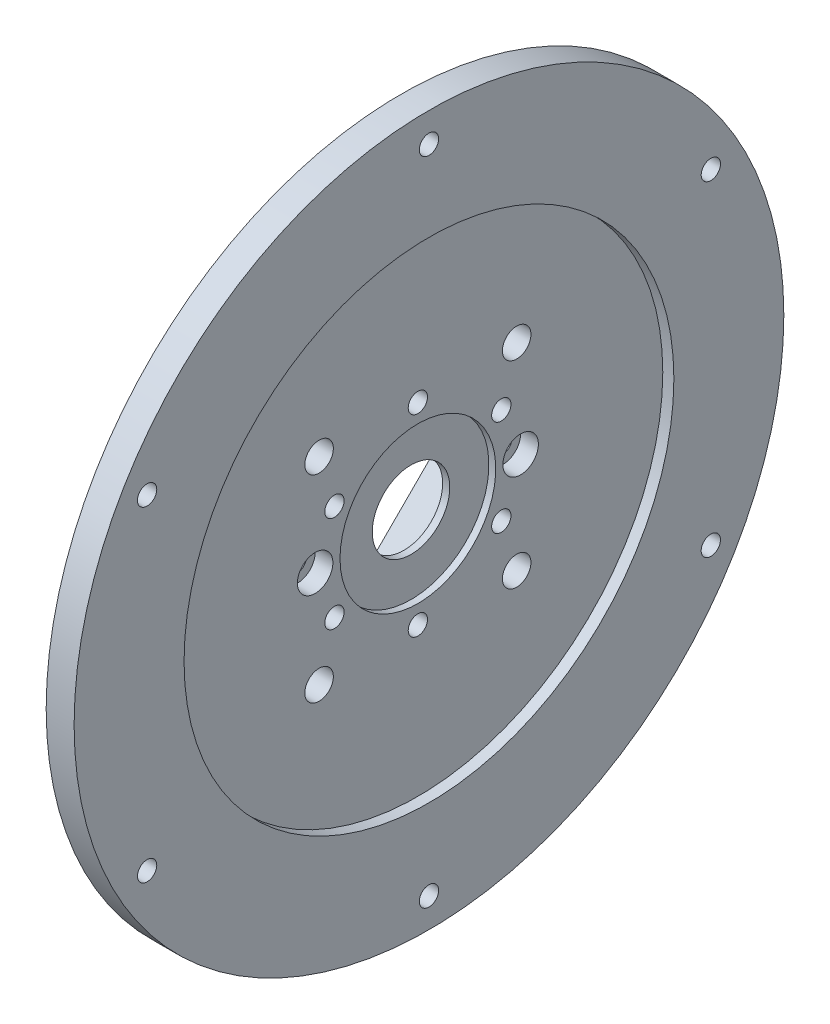
SolidWorks part; units mm, degrees
ref_plane "Front Plane" through (0, 0, 0) normal (0, 0, 1) x (1, 0, 0)
ref_plane "Top Plane" through (0, 0, 0) normal (0, 1, 0) x (1, 0, 0)
ref_plane "Right Plane" through (0, 0, 0) normal (1, 0, 0) x (0, 0, -1)
sketch "Sketch1" plane through (0, 0, 0) normal (0, 0, 1) x (1, 0, 0)
  line L0 (0, 0) -> (58.591, 0) construction
  line L2 (0, 0) -> (18.4, 0)
  line L3 (0, 0) -> (0, 2.5)
  line L4 (0, 2.5) -> (18.4, 2.5)
  line L5 (18.4, 0) -> (18.4, 2.5)
  line L6 (6.0094, 2.5) -> (6.0094, 6)
  line L11 (6.0094, 6) -> (9.9794, 6)
  line L16 (12.9794, 6) -> (12.9794, 3)
  line L17 (12.9794, 3) -> (13.6398, 3)
  line L18 (13.6398, 3) -> (13.6398, 2.5)
  line L19 (13.6398, 2.5) -> (6.0094, 2.5)
  line L22 (13.6398, 2.5) -> (16.1198, 2.5)
  line L23 (13.6398, 2.5) -> (13.6398, 4)
  line L24 (13.6398, 4) -> (16.1198, 4)
  line L25 (16.1198, 2.5) -> (16.1198, 4)
  line L27 (6.0094, 6) -> (9.9794, 6)
  line L28 (6.0094, 6) -> (6.0094, 9)
  line L29 (6.0094, 9) -> (9.9794, 9)
  line L30 (9.9794, 6) -> (9.9794, 9)
  line L31 (6.0094, 9) -> (6.0094, 8.25)
  line L32 (6.0094, 8.25) -> (5.0094, 8.25)
  line L33 (8.6609, 22.001) -> (8.6609, 12.476) construction
  line L34 (5.0094, 12.476) -> (12.3124, 12.476)
  line L35 (9.9794, 9) -> (12.3124, 9)
  line L36 (5.0094, 7.9375) -> (1.7709, 7.9375)
  line L37 (5.0094, 8.25) -> (5.0094, 12.476)
  line L38 (5.0094, 7.9375) -> (5.0094, 13.9365)
  line L39 (5.0094, 13.9365) -> (1.7709, 13.9365)
  line L40 (1.7709, 7.9375) -> (1.7709, 13.9365)
  line L41 (5.0094, 22.001) -> (12.3124, 22.001)
  line L42 (5.0094, 22.001) -> (5.0094, 30.1625)
  line L43 (5.0094, 30.1625) -> (12.3124, 30.1625)
  line L44 (12.3124, 22.001) -> (12.3124, 30.1625)
  line L49 (16.6398, 22.001) -> (16.6398, 7.5)
  line L51 (23.0198, 7.5) -> (23.0198, 6.5)
  line L54 (16.1198, 4) -> (13.6398, 4)
  line L56 (18.0398, 7.5) -> (23.0198, 7.5)
  line L57 (13.3124, 22.001) -> (16.6398, 22.001)
  line L58 (16.1198, 3.5) -> (20.0198, 3.5)
  line L59 (29.9098, 14) -> (26.9098, 11)
  line L60 (4.0094, 31.75) -> (18.0398, 31.75)
  line L61 (18.0398, 7.5) -> (23.0198, 7.5)
  line L62 (18.0398, 7.5) -> (18.0398, 12)
  line L63 (18.0398, 12) -> (23.0198, 12)
  line L64 (23.0198, 7.5) -> (23.0198, 12)
  line L65 (18.0398, 31.75) -> (18.0398, 12)
  line L66 (23.0198, 11) -> (26.9098, 11)
  line L67 (34.8098, 23) -> (31.3098, 19.5)
  line L68 (35.8098, 31) -> (38.7998, 33.99)
  line L69 (29.9098, 14) -> (29.9098, 15)
  line L70 (29.9098, 15) -> (22.9398, 15)
  line L71 (22.9398, 15) -> (21.0398, 15)
  line L72 (18.0398, 7.5) -> (16.6398, 7.5)
  line L73 (21.0398, 15) -> (21.0398, 43)
  line L74 (19.6115, 40) -> (9.6516, 40)
  line L75 (9.6516, 40) -> (4.0094, 40)
  line L76 (21.0398, 43) -> (19.6115, 43)
  line L77 (22.9398, 15) -> (29.9098, 15)
  line L78 (22.9398, 15) -> (22.9398, 21)
  line L79 (22.9398, 21) -> (29.9098, 21)
  line L80 (29.9098, 15) -> (29.9098, 21)
  line L81 (9.6516, 40) -> (19.6115, 40)
  line L82 (9.6516, 40) -> (9.6516, 50)
  line L83 (9.6516, 50) -> (19.6115, 50)
  line L84 (19.6115, 40) -> (19.6115, 50)
  line L85 (4.0094, 40) -> (4.0094, 31.75)
  line L86 (12.9794, 3) -> (12.9794, 2.5)
  line L87 (31.3098, 19.5) -> (29.9098, 19.5)
  line L88 (21.4694, 63.5) -> (21.4694, 51.308)
  line L89 (21.4694, 63.5) -> (25.9398, 63.5)
  line L90 (25.9398, 63.5) -> (25.9398, 25)
  line L91 (27.8398, 25) -> (25.9398, 25)
  line L92 (9.6516, 48) -> (8.2233, 48)
  line L93 (8.2233, 48) -> (8.2233, 53.476)
  line L94 (8.2233, 53.476) -> (19.6115, 53.476)
  line L95 (19.6115, 53.476) -> (19.6115, 50)
  line L96 (13.9174, 63.001) -> (13.9174, 53.476) construction
  line L97 (8.2233, 63.001) -> (19.6115, 63.001)
  line L98 (8.2233, 63.001) -> (8.2233, 68.2625)
  line L99 (8.2233, 68.2625) -> (19.6115, 68.2625)
  line L100 (19.6115, 63.001) -> (19.6115, 68.2625)
  line L101 (12.9794, 6) -> (11.9794, 6)
  line L102 (8.2233, 44.825) -> (4.9848, 44.825)
  line L103 (8.2233, 44.825) -> (8.2233, 54.9365)
  line L104 (8.2233, 54.9365) -> (4.9848, 54.9365)
  line L106 (9.9794, 6) -> (10.8794, 6)
  line L107 (27.8398, 25) -> (34.8098, 25)
  line L108 (34.8098, 25) -> (34.8098, 23)
  line L109 (0, 0) -> (-2, 0)
  line L110 (0, 0) -> (0, 11)
  line L111 (27.8398, 25) -> (34.8098, 25)
  line L112 (27.8398, 25) -> (27.8398, 32.5)
  line L113 (27.8398, 32.5) -> (34.8098, 32.5)
  line L114 (34.8098, 25) -> (34.8098, 32.5)
  line L115 (35.8098, 31) -> (34.8098, 31)
  line L116 (27.8398, 32.5) -> (27.8398, 64.5)
  line L117 (20.5849, 74.025) -> (6.2499, 74.025)
  line L118 (6.2499, 74.025) -> (6.2499, 76.2)
  line L119 (38.7998, 47.29) -> (30.8398, 55.25)
  line L120 (0, 11) -> (-2, 11)
  line L121 (38.7998, 43.815) -> (30.8623, 43.815)
  line L123 (-4.8152, 69.85) -> (1.5348, 76.2)
  line L124 (38.7998, 47.29) -> (38.7998, 33.99)
  line L125 (-2, 0) -> (-2, 11)
  line L126 (38.7998, 37.465) -> (30.8623, 37.465)
  line L127 (30.8623, 43.815) -> (30.8623, 37.465)
  line L128 (6.0094, 2.5) -> (6.0094, 0)
  line L129 (-0.0152, 63.5) -> (-0.0152, 30)
  line L132 (4.9848, 63.5) -> (-0.0152, 63.5)
  line L136 (-1.8152, 30) -> (-11.7752, 30)
  line L138 (-13.7752, 25.4) -> (-2, 25.4)
  line L139 (-2, 25.4) -> (-2, 11.5)
  line L140 (27.8398, 64.5) -> (20.5849, 64.5)
  line L141 (-1.8152, 30) -> (-11.7752, 30)
  line L142 (-1.8152, 30) -> (-1.8152, 39)
  line L143 (-1.8152, 39) -> (-11.7752, 39)
  line L144 (-11.7752, 30) -> (-11.7752, 39)
  line L145 (20.5849, 64.5) -> (20.5849, 74.025)
  line L146 (-12.7752, 37) -> (-12.7752, 47.29)
  line L147 (-12.7752, 37) -> (-11.7752, 37)
  line L148 (30.8398, 55.25) -> (30.8398, 76.2)
  line L149 (11.9794, 6) -> (11.9794, 5.45)
  line L154 (-2, 11.5) -> (0.5, 11.5)
  line L155 (4.9848, 60.6197) -> (24.0348, 60.6197)
  line L160 (4.9848, 60.6197) -> (4.9848, 55.8572)
  line L161 (4.9848, 55.8572) -> (24.0348, 55.8572)
  line L166 (24.0348, 60.6197) -> (24.0348, 55.8572)
  line L167 (4.9848, 60.6197) -> (24.0348, 55.8572) construction
  line L172 (4.9848, 55.8572) -> (24.0348, 60.6197) construction
  line L173 (24.0348, 62.2072) -> (25.9398, 62.2072)
  line L174 (11.9794, 5.45) -> (10.8794, 5.45)
  line L175 (10.8794, 6) -> (10.8794, 5.45)
  line L176 (24.0348, 62.2072) -> (24.0348, 54.2697)
  line L177 (24.0348, 54.2697) -> (25.9398, 54.2697)
  line L178 (25.9398, 62.2072) -> (25.9398, 54.2697)
  line L179 (24.0348, 62.2072) -> (25.9398, 54.2697) construction
  line L180 (24.0348, 54.2697) -> (25.9398, 62.2072) construction
  line L181 (3, 19.6197) -> (15.7, 19.6197)
  line L182 (3, 19.6197) -> (3, 14.8572)
  line L183 (3, 14.8572) -> (15.7, 14.8572)
  line L184 (15.7, 19.6197) -> (15.7, 14.8572)
  line L185 (3, 19.6197) -> (15.7, 14.8572) construction
  line L186 (3, 14.8572) -> (15.7, 19.6197) construction
  line L187 (15.7, 21.2072) -> (16.6398, 21.2072)
  line L188 (15.7, 21.2072) -> (15.7, 13.2697)
  line L189 (15.7, 13.2697) -> (16.6398, 13.2697)
  line L190 (16.6398, 21.2072) -> (16.6398, 13.2697)
  line L191 (15.7, 21.2072) -> (16.6398, 13.2697) construction
  line L192 (15.7, 13.2697) -> (16.6398, 21.2072) construction
  line L193 (0.5, 11.5) -> (0.5, 6.9375)
  line L194 (0.5, 6.9375) -> (1.7709, 6.9375)
  line L195 (23.0198, 6.5) -> (20.0198, 3.5)
  line L196 (4.9848, 63.5) -> (4.9848, 54.9365)
  line L197 (3, 43.825) -> (4.9848, 43.825)
  line L198 (1.7709, 6.9375) -> (1.7709, 7.9375)
  line L199 (6.0094, 0) -> (12.9794, 0)
  line L200 (12.9794, 0) -> (12.9794, 2.5)
  line L201 (18.0398, 31.75) -> (18.0398, 35.875)
  line L202 (18.0398, 35.875) -> (21.0398, 35.875)
  line L203 (30.8398, 76.2) -> (6.2499, 76.2)
  line L204 (2.8049, 69.85) -> (7.2499, 69.85) construction
  line L205 (7.2499, 67.4688) -> (26.2999, 67.4688)
  line L206 (7.2499, 74.025) -> (7.2499, 64.5)
  line L207 (7.2499, 64.5) -> (-1.8152, 64.5)
  line L208 (-1.8152, 64.5) -> (-1.8152, 39)
  line L209 (-12.7752, 47.29) -> (-4.8152, 55.25)
  line L210 (-4.8152, 55.25) -> (-4.8152, 69.85)
  line L211 (7.2499, 67.4688) -> (7.2499, 72.2312)
  line L212 (7.2499, 72.2312) -> (26.2999, 72.2313)
  line L213 (26.2999, 67.4688) -> (26.2999, 72.2313)
  line L214 (26.2999, 73.8187) -> (30.8398, 73.8187)
  line L215 (26.2999, 73.8187) -> (26.2999, 65.8813)
  line L216 (26.2999, 65.8813) -> (30.8398, 65.8813)
  line L217 (30.8398, 73.8187) -> (30.8398, 65.8813)
  line L218 (2.8049, 72.2313) -> (25.0299, 72.2313)
  line L219 (2.8049, 72.2313) -> (2.8049, 67.4687)
  line L220 (2.8049, 67.4687) -> (25.0299, 67.4687)
  line L221 (25.0299, 72.2313) -> (25.0299, 67.4687)
  line L222 (25.0299, 69.85) -> (20.5849, 69.85) construction
  line L223 (21.4694, 51.308) -> (22.9398, 51.308)
  line L224 (22.9398, 51.308) -> (22.9398, 21)
  line L225 (13.6398, 4) -> (13.6398, 12.2697)
  line L226 (13.6398, 12.2697) -> (13.3124, 12.2697)
  line L227 (13.3124, 12.2697) -> (13.3124, 22.001)
  line L228 (12.3124, 9) -> (12.3124, 12.476)
  line L229 (-1.8152, 30) -> (-0.0152, 30)
  line L230 (8.2233, 65.6317) -> (2.8049, 65.6317) construction
  line L231 (19.6115, 65.6317) -> (25.0299, 65.6317) construction
  line L232 (1.5348, 76.2) -> (6.2499, 76.2)
  line L233 (-11.7752, 30) -> (-13.7752, 30)
  line L234 (-13.7752, 30) -> (-13.7752, 25.4)
  line L235 (3, 13.9365) -> (3, 43.825)
  line L236 (4.9848, 54.9365) -> (4.9848, 44.825)
  line L237 (4.9848, 43.825) -> (4.9848, 44.825)
  circle A0 centre (26.8898, 25.95) radius 0.95
  circle A1 centre (21.9898, 15.95) radius 0.95
  circle A2 centre (17.3398, 8.2) radius 0.7
  circle A3 centre (10.4294, 6.45) radius 0.45
  circle A4 centre (-0.9152, 30.9) radius 0.9
  point P7 (24.9873, 58.2385)
  point P131 (16.1699, 17.2385)
  point P135 (14.5098, 58.2385)
  point P146 (9.35, 17.2385)
sketch "Sketch2" plane through (0, 0, 0) normal (0, 0, 1) x (1, 0, 0)
  line L0 (-1.8152, 30) -> (-11.7752, 30) construction
  line L1 (-2, 25.4) -> (-2, 11.5) construction
  line L3 (-13.7752, 25.4) -> (-2, 25.4) construction
  line L4 (-2, 11.5) -> (0.5, 11.5) construction
  line L5 (0.5, 11.5) -> (0.5, 6.9375) construction
  line L6 (0.5, 6.9375) -> (1.7709, 6.9375) construction
  line L10 (4.9848, 63.5) -> (-0.0152, 63.5) construction
  line L11 (-0.0152, 63.5) -> (-0.0152, 30) construction
  line L14 (-1.8152, 30) -> (-11.7752, 30)
  line L15 (-2, 25.4) -> (-2, 11.5)
  line L17 (-13.7752, 25.4) -> (-2, 25.4)
  line L18 (-2, 11.5) -> (0.5, 11.5)
  line L19 (0.5, 11.5) -> (0.5, 6.9375)
  line L20 (0.5, 6.9375) -> (1.7709, 6.9375)
  line L24 (4.9848, 63.5) -> (-0.0152, 63.5)
  line L25 (-0.0152, 63.5) -> (-0.0152, 30)
  line L28 (-1.8152, 30) -> (-0.0152, 30) construction
  line L29 (-1.8152, 30) -> (-0.0152, 30)
  line L30 (-13.7752, 30) -> (-13.7752, 25.4) construction
  line L31 (-11.7752, 30) -> (-13.7752, 30) construction
  line L32 (-13.7752, 30) -> (-13.7752, 25.4)
  line L33 (-11.7752, 30) -> (-13.7752, 30)
  line L34 (1.7709, 6.9375) -> (1.7709, 7.9375) construction
  line L35 (1.7709, 7.9375) -> (1.7709, 13.9365) construction
  line L36 (5.0094, 13.9365) -> (1.7709, 13.9365) construction
  line L37 (3, 13.9365) -> (3, 43.825) construction
  line L40 (4.9848, 63.5) -> (4.9848, 54.9365) construction
  line L41 (1.7709, 6.9375) -> (1.7709, 7.9375)
  line L42 (1.7709, 7.9375) -> (1.7709, 13.9365)
  line L43 (3, 13.9365) -> (1.7709, 13.9365)
  line L44 (3, 13.9365) -> (3, 43.825)
  line L47 (4.9848, 63.5) -> (4.9848, 54.9365)
  line L48 (4.9848, 43.825) -> (4.9848, 44.825) construction
  line L49 (3, 43.825) -> (4.9848, 43.825) construction
  line L50 (4.9848, 54.9365) -> (4.9848, 44.825) construction
  line L51 (4.9848, 43.825) -> (4.9848, 44.825)
  line L52 (3, 43.825) -> (4.9848, 43.825)
  line L53 (4.9848, 54.9365) -> (4.9848, 44.825)
revolve "Revolve1" add sketch "Sketch2" angle 360 about L0
sketch "Sketch3" plane through (0, 0, 0) normal (1, 0, 0) x (0, 0, -1)
  line L0 (0, 0) -> (0, 69.85) construction
  line L1 (0, 0) -> (13.6271, 68.5079) construction
  line L2 (0, 0) -> (0, 58.2385) construction
  line L3 (0, 0) -> (50.436, 29.1192) construction
  line L4 (0, 0) -> (0, 31.75) construction
  line L5 (0, 0) -> (12.1502, 29.3332) construction
  line L6 (0, 0) -> (0, 17.2385) construction
  line L7 (0, 0) -> (14.929, 8.6192) construction
  line L8 (0, 0) -> (0, 58.2385) construction
  line L9 (0, 0) -> (50.436, 29.1192) construction
  line L10 (0, 0) -> (5.9583, 29.9542) construction
  line L11 (0, 0) -> (16.9677, 25.394) construction
  circle A0 centre (0, 0) radius 69.85 construction
  circle A1 centre (0, 0) radius 58.2385 construction
  circle A2 centre (0, 0) radius 31.75 construction
  circle A3 centre (0, 0) radius 17.2385 construction
  circle A4 centre (0, 69.85) radius 3.175
  circle A5 centre (0, 58.2385) radius 4.7625
  circle A6 centre (0, 31.75) radius 3.175
  circle A7 centre (0, 17.2385) radius 4.7625
  circle A8 centre (13.6271, 68.5079) radius 3.175
  circle A9 centre (26.7304, 64.533) radius 3.175
  circle A10 centre (38.8066, 58.0782) radius 3.175
  circle A11 centre (49.3914, 49.3914) radius 3.175
  circle A12 centre (58.0782, 38.8066) radius 3.175
  circle A13 centre (64.533, 26.7304) radius 3.175
  circle A14 centre (68.5079, 13.6271) radius 3.175
  circle A15 centre (69.85, 0) radius 3.175
  circle A16 centre (68.5079, -13.6271) radius 3.175
  circle A17 centre (64.533, -26.7304) radius 3.175
  circle A18 centre (58.0782, -38.8066) radius 3.175
  circle A19 centre (49.3914, -49.3914) radius 3.175
  circle A20 centre (38.8066, -58.0782) radius 3.175
  circle A21 centre (26.7304, -64.533) radius 3.175
  circle A22 centre (13.6271, -68.5079) radius 3.175
  circle A23 centre (0, -69.85) radius 3.175
  circle A24 centre (-13.6271, -68.5079) radius 3.175
  circle A25 centre (-26.7304, -64.533) radius 3.175
  circle A26 centre (-38.8066, -58.0782) radius 3.175
  circle A27 centre (-49.3914, -49.3914) radius 3.175
  circle A28 centre (-58.0782, -38.8066) radius 3.175
  circle A29 centre (-64.533, -26.7304) radius 3.175
  circle A30 centre (-68.5079, -13.6271) radius 3.175
  circle A31 centre (-69.85, 0) radius 3.175
  circle A32 centre (-68.5079, 13.6271) radius 3.175
  circle A33 centre (-64.533, 26.7304) radius 3.175
  circle A34 centre (-58.0782, 38.8066) radius 3.175
  circle A35 centre (-49.3914, 49.3914) radius 3.175
  circle A36 centre (-38.8066, 58.0782) radius 3.175
  circle A37 centre (-26.7304, 64.533) radius 3.175
  circle A38 centre (-13.6271, 68.5079) radius 3.175
  circle A47 centre (50.436, 29.1192) radius 4.7625
  circle A48 centre (50.436, -29.1192) radius 4.7625
  circle A49 centre (0, -58.2385) radius 4.7625
  circle A50 centre (-50.436, -29.1192) radius 4.7625
  circle A51 centre (-50.436, 29.1192) radius 4.7625
  circle A58 centre (12.1502, 29.3332) radius 3.175
  circle A59 centre (22.4506, 22.4506) radius 3.175
  circle A60 centre (29.3332, 12.1502) radius 3.175
  circle A61 centre (31.75, 0) radius 3.175
  circle A62 centre (29.3332, -12.1502) radius 3.175
  circle A63 centre (22.4506, -22.4506) radius 3.175
  circle A64 centre (12.1502, -29.3332) radius 3.175
  circle A65 centre (0, -31.75) radius 3.175
  circle A66 centre (-12.1502, -29.3332) radius 3.175
  circle A67 centre (-22.4506, -22.4506) radius 3.175
  circle A68 centre (-29.3332, -12.1502) radius 3.175
  circle A69 centre (-31.75, 0) radius 3.175
  circle A70 centre (-29.3332, 12.1502) radius 3.175
  circle A71 centre (-22.4506, 22.4506) radius 3.175
  circle A72 centre (14.929, 8.6192) radius 4.7625
  circle A73 centre (14.929, -8.6192) radius 4.7625
  circle A74 centre (0, -17.2385) radius 4.7625
  circle A75 centre (-14.929, -8.6192) radius 4.7625
  circle A76 centre (-14.929, 8.6192) radius 4.7625
  circle A77 centre (0, 0) radius 50
  circle A78 centre (0, 0) radius 9
  circle A79 centre (-12.1502, 29.3332) radius 3.175
  circle A80 centre (0, 0) radius 76.2
  circle A81 centre (0, 0) radius 74.025
  circle A82 centre (0, 69.85) radius 3.9687
  circle A83 centre (49.3914, 49.3914) radius 3.9687
  circle A84 centre (69.85, 0) radius 3.9688
  circle A85 centre (49.3914, -49.3914) radius 3.9687
  circle A86 centre (0, -69.85) radius 3.9687
  circle A87 centre (-49.3914, -49.3914) radius 3.9687
  circle A88 centre (-69.85, 0) radius 3.9688
  circle A89 centre (-49.3914, 49.3914) radius 3.9687
  circle A90 centre (0, 69.85) radius 2.3812
  circle A91 centre (13.6271, 68.5079) radius 2.3812
  circle A92 centre (26.7304, 64.533) radius 2.3813
  circle A93 centre (38.8066, 58.0782) radius 2.3812
  circle A94 centre (49.3914, 49.3914) radius 2.3812
  circle A95 centre (58.0782, 38.8066) radius 2.3812
  circle A96 centre (64.533, 26.7304) radius 2.3813
  circle A97 centre (68.5079, 13.6271) radius 2.3813
  circle A98 centre (69.85, 0) radius 2.3813
  circle A99 centre (68.5079, -13.6271) radius 2.3813
  circle A100 centre (64.533, -26.7304) radius 2.3813
  circle A101 centre (58.0782, -38.8066) radius 2.3812
  circle A102 centre (49.3914, -49.3914) radius 2.3812
  circle A103 centre (38.8066, -58.0782) radius 2.3812
  circle A104 centre (26.7304, -64.533) radius 2.3813
  circle A105 centre (13.6271, -68.5079) radius 2.3812
  circle A106 centre (0, -69.85) radius 2.3812
  circle A107 centre (-13.6271, -68.5079) radius 2.3812
  circle A108 centre (-26.7304, -64.533) radius 2.3813
  circle A109 centre (-38.8066, -58.0782) radius 2.3812
  circle A110 centre (-49.3914, -49.3914) radius 2.3812
  circle A111 centre (-58.0782, -38.8066) radius 2.3812
  circle A112 centre (-64.533, -26.7304) radius 2.3812
  arc A113 (3.0399, 30.8338) -> (8.9911, 29.65) centre (5.9583, 29.9542) cw
  arc A114 (14.6081, 27.3234) -> (19.6532, 23.9523) centre (16.9677, 25.394) cw
  arc A115 (23.9523, 19.6532) -> (27.3234, 14.6081) centre (25.394, 16.9677) cw
  arc A116 (29.65, 8.9911) -> (30.8338, 3.0399) centre (29.9542, 5.9583) cw
  arc A117 (30.8338, -3.0399) -> (29.65, -8.9911) centre (29.9542, -5.9583) cw
  arc A118 (27.3234, -14.6081) -> (23.9523, -19.6532) centre (25.394, -16.9677) cw
  arc A119 (19.6532, -23.9523) -> (14.6081, -27.3234) centre (16.9677, -25.394) cw
  arc A120 (8.9911, -29.65) -> (3.0399, -30.8338) centre (5.9583, -29.9542) cw
  arc A121 (-3.0399, -30.8338) -> (-8.9911, -29.65) centre (-5.9583, -29.9542) cw
  arc A122 (-14.6081, -27.3234) -> (-19.6532, -23.9523) centre (-16.9677, -25.394) cw
  arc A123 (-23.9523, -19.6532) -> (-27.3234, -14.6081) centre (-25.394, -16.9677) cw
  arc A124 (-29.65, -8.9911) -> (-30.8338, -3.0399) centre (-29.9542, -5.9583) cw
  arc A125 (-30.8338, 3.0399) -> (-29.65, 8.9911) centre (-29.9542, 5.9583) cw
  arc A126 (-27.3234, 14.6081) -> (-23.9523, 19.6532) centre (-25.394, 16.9677) cw
  arc A127 (-19.6532, 23.9523) -> (-14.6081, 27.3234) centre (-16.9677, 25.394) cw
  arc A128 (-8.9911, 29.65) -> (-3.0399, 30.8338) centre (-5.9583, 29.9542) cw
  arc A129 (26.9875, 0) -> (26.9932, 0.1932) centre (30.2705, 0) cw
  arc A130 (65.0988, 0.2771) -> (65.0875, 0) centre (68.4964, 0) ccw
  circle A131 centre (1.5875, 0) radius 40
  circle A132 centre (1.5875, 0) radius 2.5
  circle A133 centre (1.5875, 0) radius 3
  circle A134 centre (1.5875, 0) radius 43
  circle A135 centre (-68.5079, -13.6271) radius 2.3813
  circle A136 centre (-69.85, 0) radius 2.3813
  circle A137 centre (-68.5079, 13.6271) radius 2.3813
  circle A138 centre (-64.533, 26.7304) radius 2.3812
  circle A139 centre (-58.0782, 38.8066) radius 2.3812
  circle A140 centre (-49.3914, 49.3914) radius 2.3812
  circle A141 centre (-38.8066, 58.0782) radius 2.3812
  circle A142 centre (-26.7304, 64.533) radius 2.3813
  circle A143 centre (-13.6271, 68.5079) radius 2.3812
  circle A144 centre (0, 58.2385) radius 2.3812
  circle A145 centre (0, 58.2385) radius 3.9688
  circle A146 centre (50.436, 29.1192) radius 3.9688
  circle A147 centre (50.436, 29.1192) radius 2.3813
  circle A148 centre (50.436, -29.1192) radius 3.9687
  circle A149 centre (50.436, -29.1192) radius 2.3812
  circle A150 centre (0, -58.2385) radius 3.9687
  circle A151 centre (0, -58.2385) radius 2.3812
  circle A152 centre (-50.436, -29.1192) radius 3.9687
  circle A153 centre (-50.436, -29.1192) radius 2.3812
  circle A154 centre (-50.436, 29.1192) radius 3.9687
  circle A155 centre (-50.436, 29.1192) radius 2.3812
  spline S1 degree 4 number of poles 499 (26.9875, 0) -> (26.9932, 0.1932)
  spline S3 degree 4 number of poles 617 (65.0875, 0) -> (65.0988, 0.2771)
  point P116 (0, 0)
  point P225 (0, 0)
sketch "Sketch4" plane through (0, 0, 0) normal (1, 0, 0) x (0, 0, -1)
  circle A0 centre (-14.929, -8.6192) radius 4.7625 construction
  circle A1 centre (-14.929, 8.6192) radius 4.7625 construction
  circle A2 centre (0, 17.2385) radius 4.7625 construction
  circle A3 centre (14.929, 8.6192) radius 4.7625 construction
  circle A4 centre (14.929, -8.6192) radius 4.7625 construction
  circle A5 centre (0, -17.2385) radius 4.7625 construction
  circle A6 centre (0, -58.2385) radius 4.7625 construction
  circle A7 centre (-50.436, -29.1192) radius 4.7625 construction
  circle A8 centre (50.436, -29.1192) radius 4.7625 construction
  circle A9 centre (50.436, 29.1192) radius 4.7625 construction
  circle A10 centre (0, 58.2385) radius 4.7625 construction
  circle A11 centre (-50.436, 29.1192) radius 4.7625 construction
  circle A12 centre (-14.929, -8.6192) radius 4.7625
  circle A13 centre (-14.929, 8.6192) radius 4.7625
  circle A14 centre (0, 17.2385) radius 4.7625
  circle A15 centre (14.929, 8.6192) radius 4.7625
  circle A16 centre (14.929, -8.6192) radius 4.7625
  circle A17 centre (0, -17.2385) radius 4.7625
  circle A18 centre (0, -58.2385) radius 4.7625
  circle A19 centre (-50.436, -29.1192) radius 4.7625
  circle A20 centre (50.436, -29.1192) radius 4.7625
  circle A21 centre (50.436, 29.1192) radius 4.7625
  circle A22 centre (0, 58.2385) radius 4.7625
  circle A23 centre (-50.436, 29.1192) radius 4.7625
  circle A24 centre (0, 58.2385) radius 1.7272
  circle A25 centre (50.436, 29.1192) radius 1.7272
  circle A26 centre (50.436, -29.1192) radius 1.7272
  circle A27 centre (0, -58.2385) radius 1.7272
  circle A28 centre (-50.436, -29.1192) radius 1.7272
  circle A29 centre (-50.436, 29.1192) radius 1.7272
  circle A30 centre (-14.929, 8.6192) radius 1.7272
  circle A31 centre (0, 17.2385) radius 1.7272
  circle A32 centre (14.929, 8.6192) radius 1.7272
  circle A33 centre (14.929, -8.6192) radius 1.7272
  circle A34 centre (0, -17.2385) radius 1.7272
  circle A35 centre (-14.929, -8.6192) radius 1.7272
  dimension "D1" = 3.4544
extrude "Cut-Extrude1" cut sketch "Sketch4" against normal through all and the other way through all contours A29 | A30 | A31 | A32 | A33 | A34 | A35 | A25 | A26 | A24 | A28 | A27
sketch "Sketch5" plane through (3, 0, 0) normal (1, 0, 0) x (0, 0, -1)
  line L0 (-18.385, 0) -> (0, 0) construction
  line L1 (0, 0) -> (18.385, 0) construction
  circle A0 centre (-18.385, 0) radius 1.5875
  circle A1 centre (18.385, 0) radius 1.5875
  dimension "D2" = 3.175
  dimension "D1" = 36.77
extrude "Cut-Extrude2" cut sketch "Sketch5" against normal through all
sketch "Sketch6" plane through (3, 0, 0) normal (1, 0, 0) x (0, 0, -1)
  circle A0 centre (-18.385, 0) radius 3.175
  circle A1 centre (18.385, 0) radius 3.175
  dimension "D1" = 6.35
extrude "Cut-Extrude3" cut sketch "Sketch6" against normal blind 3.175
sketch "Sketch7" plane through (-13.7752, 0, 0) normal (-1, 0, 0) x (0, 0, 1)
  line L0 (3.0706, 25.2137) -> (25.2137, 3.0706)
  line L1 (25.2137, -3.0706) -> (3.0706, -25.2137)
  line L2 (-3.0706, -25.2137) -> (-25.2137, -3.0706)
  line L3 (-25.2137, 3.0706) -> (-3.0706, 25.2137)
  circle A3 centre (0, 0) radius 25.4 construction
  circle A4 centre (0, 0) radius 25.4
  point P15 (0, 0)
  circle M5 centre (0, 0) radius 25.4
  dimension "D2" = 40
  dimension "D1" = 4
extrude "Boss-Extrude1" add sketch "Sketch7" against normal up to next contours L0 M5 | L3 M5 | L2 M5 | L1 M5
fillet "Fillet1" radius 3.175 8 edges at (-7.8876, -25.2137, -3.0706) (-7.8876, -3.0706, -25.2137) (-7.8876, -3.0706, 25.2137) (-7.8876, -25.2137, 3.0706) (-7.8876, 25.2137, 3.0706) (-7.8876, 3.0706, 25.2137) (-7.8876, 3.0706, -25.2137) (-7.8876, 25.2137, -3.0706)
sketch "Sketch8" plane through (-13.7752, 0, 0) normal (-1, 0, 0) x (0, 0, 1)
  line L0 (0, 0) -> (17.6777, 17.6777) construction
  line L1 (0, 0) -> (13.9248, 0) construction
  line L2 (17.6777, 17.6777) -> (21.2132, 21.2132) construction
  line L3 (17.6777, 17.6777) -> (14.1421, 14.1421) construction
  line L7 (3.874, 24.4103) -> (24.4103, 3.874) construction
  circle A0 centre (17.6777, 17.6777) radius 2.5527
  circle A1 centre (0, 0) radius 30 construction
  circle A2 centre (17.6777, -17.6777) radius 2.5527
  circle A3 centre (-17.6777, -17.6777) radius 2.5527
  circle A4 centre (-17.6777, 17.6777) radius 2.5527
  point P20 (0, 0)
  dimension "D2" = 5.1054
  dimension "D1" = 45
  dimension "D3" = 4
extrude "Cut-Extrude4" cut sketch "Sketch8" against normal through all
